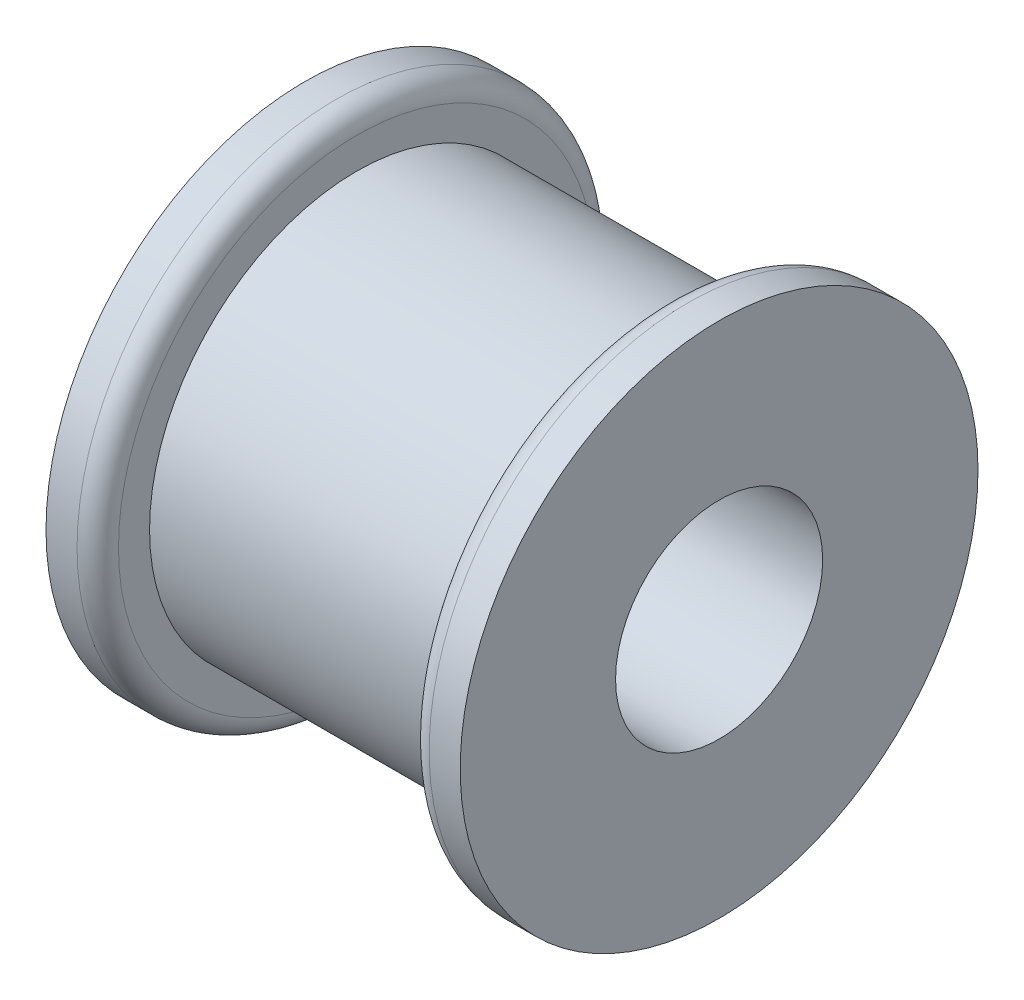
SolidWorks part; units mm, degrees
ref_plane "Front" through (0, 0, 0) normal (0, 0, 1) x (1, 0, 0)
ref_plane "Top" through (0, 0, 0) normal (0, 1, 0) x (1, 0, 0)
ref_plane "Right" through (0, 0, 0) normal (1, 0, 0) x (0, 0, -1)
sketch "Sketch1" plane through (0, 0, 0) normal (1, 0, 0) x (0, 0, -1)
  circle A0 centre (0, 0) radius 12.7
  dimension "D1" = 25.4
extrude "Boss-Extrude1" add sketch "Sketch1" along normal blind 19.05
sketch "Sketch2" plane through (0, 0, 0) normal (-1, 0, 0) x (0, 0, 1)
  circle A0 centre (0, 0) radius 15.875
  circle A1 centre (0, 0) radius 12.7 construction
  dimension "D1" = 3.175
extrude "Boss-Extrude2" add sketch "Sketch2" along normal blind 3.175
sketch "Sketch3" plane through (19.05, 0, 0) normal (1, 0, 0) x (0, 0, -1)
  circle A0 centre (0, 0) radius 15.875 construction
  circle A1 centre (0, 0) radius 15.875
extrude "Boss-Extrude3" add sketch "Sketch3" along normal blind 3.175
sketch "Sketch4" plane through (-3.175, 0, 0) normal (-1, 0, 0) x (0, 0, 1)
  circle A0 centre (0, 0) radius 6.35
  dimension "D1" = 12.7
extrude "Cut-Extrude1" cut sketch "Sketch4" against normal through all
fillet "Fillet1" radius 1.27 2 edges at (0, 0, 15.875) (19.05, 0, -15.875)
ref_plane "Mid_Plane" through (9.525, 0, 0) normal (-1, 0, 0) x (0, 0, 1)
